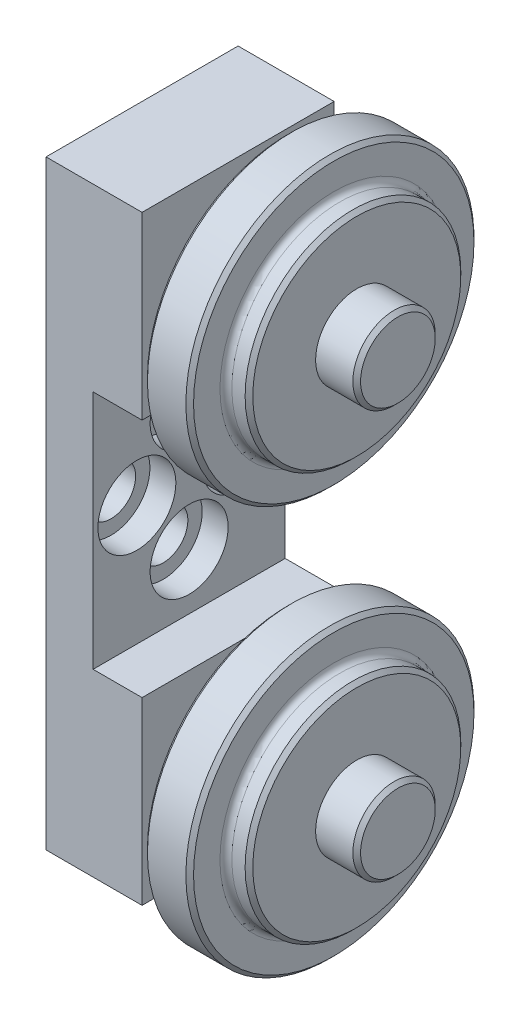
SolidWorks part; units mm, degrees
ref_plane "Front" through (0, 0, 0) normal (0, 0, 1) x (1, 0, 0)
ref_plane "Top" through (0, 0, 0) normal (0, 1, 0) x (1, 0, 0)
ref_plane "Right" through (0, 0, 0) normal (1, 0, 0) x (0, 0, -1)
sketch "Sketch2" plane through (0, 0, 0) normal (0, 0, 1) x (1, 0, 0)
  line L0 (3.048, 42.037) -> (3.048, 45.5295)
  line L1 (3.048, 45.5295) -> (2.54, 46.0375)
  line L2 (2.54, 46.0375) -> (-2.54, 46.0375)
  line L3 (-2.54, 46.0375) -> (-3.048, 45.5295)
  line L4 (-3.048, 45.5295) -> (-3.048, 42.037)
  line L5 (-3.8354, 41.2496) -> (-5.588, 41.2496)
  line L6 (-5.588, 41.2496) -> (-6.096, 40.7416)
  line L7 (-6.096, 40.7416) -> (-6.096, 30.1625)
  line L8 (0, 46.0375) -> (0, 7.9375) construction
  line L9 (-6.607, 30.1625) -> (-6.096, 30.1625)
  line L10 (6.096, 32.4358) -> (6.096, 21.5392) construction
  line L11 (6.096, 32.4358) -> (6.096, 40.7416)
  line L12 (6.096, 40.7416) -> (5.588, 41.2496)
  line L13 (5.588, 41.2496) -> (3.8354, 41.2496)
  line L14 (4.7117, 41.2496) -> (4.7117, 12.7254) construction
  line L15 (-8.1041, 34.8869) -> (-8.1041, 19.0881) construction
  line L16 (-9.6012, 30.1625) -> (-17.1704, 30.1625)
  line L17 (-17.1704, 30.1625) -> (-17.6784, 29.6545)
  line L18 (-17.6784, 29.6545) -> (-17.6784, 26.9875)
  line L19 (-13.3858, 30.1625) -> (-13.3858, 23.8125) construction
  line L20 (0, 26.9875) -> (0, -26.9875) construction
  line L29 (11.5316, 26.9875) -> (11.5316, 31.9278)
  line L30 (11.5316, 31.9278) -> (11.0236, 32.4358)
  line L31 (11.0236, 32.4358) -> (6.096, 32.4358)
  line L37 (-6.607, 30.1625) -> (-6.607, 34.8869)
  line L38 (-6.607, 34.8869) -> (-9.6012, 34.8869)
  line L39 (-9.6012, 34.8869) -> (-9.6012, 30.1625)
  line L62 (-17.6784, 26.9875) -> (11.5316, 26.9875)
  arc A0 (-3.8354, 41.2496) -> (-3.048, 42.037) centre (-3.8354, 42.037) ccw
  arc A1 (3.048, 42.037) -> (3.8354, 41.2496) centre (3.8354, 42.037) ccw
  point P11 (6.096, 26.9875)
  point P12 (0, 26.9875)
  point P22 (4.7117, 26.9875)
  point P25 (-8.1041, 26.9875)
  point P30 (-13.3858, 26.9875)
  dimension "D3" = 0.7874
  dimension "D1" = 45
  dimension "D2" = 0.508
  dimension "Wheel Thick 1" = 6.096
  dimension "Wheel Thick 2" = 12.192
  dimension "D4" = 0.511
  dimension "Wheel Dia 1" = 38.1
  dimension "Wheel Dia 3" = 10.8966
  dimension "Wheel Dia 2" = 28.5242
  dimension "Wheel Dia 4" = 15.7988
  dimension "Wheel Dia 5" = 6.35
  dimension "Wheel Wd 1" = 21.1328
  dimension "Nose Wd" = 5.4356
  dimension "Wheel Wd 2" = 29.21
  dimension "Center-To-Center" = 53.975
revolve "Revolve1" add sketch "Sketch2" angle 360 mid plane about L62
sketch "Sketch1" plane through (0, 0, 0) normal (0, 0, 1) x (1, 0, 0)
  line L0 (-22.3012, 39.6875) -> (-22.3012, -39.6875)
  line L1 (-22.3012, -39.6875) -> (-9.6012, -39.6875)
  line L2 (-9.6012, -39.6875) -> (-9.6012, -15.8877)
  line L3 (-9.6012, -15.8877) -> (-16.0782, -15.8877)
  line L4 (-16.0782, -15.8877) -> (-16.0782, 15.8877)
  line L5 (-16.0782, 15.8877) -> (-9.6012, 15.8877)
  line L6 (-9.6012, 15.8877) -> (-9.6012, 39.6875)
  line L7 (-9.6012, 39.6875) -> (-22.3012, 39.6875)
  line L9 (-9.6012, 34.8869) -> (-9.6012, 19.0881) construction
  point P8 (-22.3012, 0)
  dimension "Body Dp" = 12.7
  dimension "Body Ht" = 79.375
  dimension "Neck Wd" = 6.223
  dimension "Nose Ht" = 23.7998
extrude "Boss-Extrude1" add sketch "Sketch1" along normal mid plane 25.4 separate body
sketch "Sketch3" plane through (-22.3012, 0, 0) normal (-1, 0, 0) x (0, 0, 1)
  line L0 (0, 26.9875) -> (0, -26.9875) construction
  circle A0 centre (0, 26.9875) radius 3.175
  circle A1 centre (0, -26.9875) radius 3.175
  circle A2 centre (0, 26.9875) radius 3.175 construction
extrude "Cut-Extrude1" cut sketch "Sketch3" against normal through all
mirror "Mirror1" about plane through (0, 0, 0) normal (0, 1, 0) of bodies 109
sketch "Sketch4" plane through (-16.0782, 0, 0) normal (1, 0, 0) x (0, 0, -1)
  line L0 (0, 8.4963) -> (0, -8.4963) construction
  line L2 (-6.9088, 0) -> (6.9088, 0) construction
  circle A0 centre (0, 8.4963) radius 3.2639
  circle A1 centre (0, -8.4963) radius 3.2639
  circle A2 centre (-6.9088, 0) radius 3.2639
  circle A3 centre (6.9088, 0) radius 3.2639
  dimension "Inner Dia" = 6.5278
  dimension "Holes Vert" = 16.9926
  dimension "Holes Hor" = 13.8176
extrude "Cut-Extrude2" cut sketch "Sketch4" against normal through all
sketch "Sketch5" plane through (-16.0782, 0, 0) normal (1, 0, 0) x (0, 0, -1)
  circle A0 centre (0, 8.4963) radius 5.1562
  circle A1 centre (6.9088, 0) radius 5.1562
  circle A2 centre (-6.9088, 0) radius 5.1562
  circle A3 centre (0, -8.4963) radius 5.1562
  dimension "Outer Dia" = 10.3124
extrude "Cut-Extrude3" cut sketch "Sketch5" against normal blind 3.429
sketch "Sketch6" plane through (0, 0, 0) normal (0, 0, 1) x (1, 0, 0)
  line L0 (-19.5072, -5.1562) -> (-16.0782, -5.1562) construction
  line L1 (-22.3012, -3.2639) -> (-19.5072, -3.2639) construction
  line L2 (-19.5072, -5.1562) -> (-19.5072, 5.1562) construction
  line L3 (-16.0782, 5.1562) -> (-19.5072, 5.1562) construction
  line L4 (-19.5072, 3.2639) -> (-22.3012, 3.2639) construction
  line L5 (-19.5072, -5.1562) -> (-16.0782, -5.1562)
  line L6 (-22.3012, -3.2639) -> (-19.5072, -3.2639)
  line L7 (-19.5072, -5.1562) -> (-19.5072, 5.1562)
  line L8 (-16.0782, 5.1562) -> (-19.5072, 5.1562)
  line L9 (-19.5072, 3.2639) -> (-22.3012, 3.2639)
